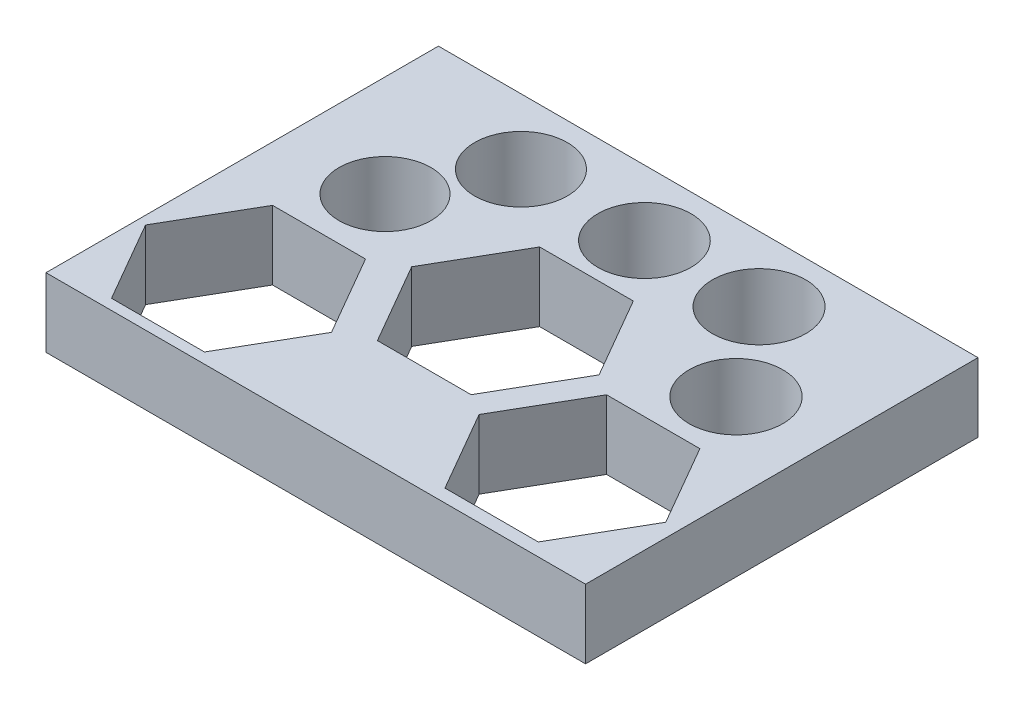
SolidWorks part; units mm, degrees
ref_plane "Front Plane" through (0, 0, 0) normal (0, 0, 1) x (1, 0, 0)
ref_plane "Top Plane" through (0, 0, 0) normal (0, 1, 0) x (1, 0, 0)
ref_plane "Right Plane" through (0, 0, 0) normal (1, 0, 0) x (0, 0, -1)
sketch "Sketch1" plane through (0, 0, 0) normal (0, 1, 0) x (1, 0, 0)
  line L1 (0, 0) -> (23.4547, 0)
  line L2 (0, 0) -> (0, 17.059)
  line L3 (0, 17.059) -> (23.4547, 17.059)
  line L4 (23.4547, 0) -> (23.4547, 17.059)
  line L5 (6.4297, 7.4595) -> (2.3883, 7.4595)
  line L6 (2.3883, 7.4595) -> (0.3676, 3.9595)
  line L7 (0.3676, 3.9595) -> (2.3883, 0.4595)
  line L8 (2.3883, 0.4595) -> (6.4297, 0.4595)
  line L9 (6.4297, 0.4595) -> (8.4505, 3.9595)
  line L10 (8.4505, 3.9595) -> (6.4297, 7.4595)
  line L11 (13.8319, 11.6985) -> (9.7604, 11.6985)
  line L12 (9.7604, 11.6985) -> (7.7247, 8.1725)
  line L13 (7.7247, 8.1725) -> (9.7604, 4.6465)
  line L14 (9.7604, 4.6465) -> (13.8319, 4.6465)
  line L15 (13.8319, 4.6465) -> (15.8676, 8.1725)
  line L16 (15.8676, 8.1725) -> (13.8319, 11.6985)
  line L17 (20.8364, 7.5879) -> (16.78, 7.5879)
  line L18 (16.78, 7.5879) -> (14.7517, 4.0749)
  line L19 (14.7517, 4.0749) -> (16.78, 0.562)
  line L20 (16.78, 0.562) -> (20.8364, 0.562)
  line L21 (20.8364, 0.562) -> (22.8646, 4.0749)
  line L22 (22.8646, 4.0749) -> (20.8364, 7.5879)
  circle A0 centre (4.409, 10.3275) radius 2
  circle A1 centre (6.4297, 14.2168) radius 2.015
  circle A2 centre (16.78, 14.2168) radius 2.03
  circle A3 centre (11.7962, 14.2168) radius 2.025
  circle A4 centre (19.6651, 10.3275) radius 2.035
  circle A5 centre (4.409, 3.9595) radius 4.0414 construction
  circle A6 centre (11.7962, 8.1725) radius 4.0714 construction
  circle A7 centre (18.8082, 4.0749) radius 4.0565 construction
  point P24 (22.2132, 3.0298)
  point P40 (14.5254, 7.4222)
  point P41 (5.1016, 4.5655)
  point P42 (4.409, 3.9595)
  point P43 (11.7962, 8.1725)
  point P44 (18.8082, 4.0749)
  point P45 (18.8082, 11.6985)
  point P46 (19.316, 11.1253)
  point P47 (4.008, 11.1253)
  point P48 (15.4766, 14.2168)
  point P49 (11.1883, 14.2168)
  point P50 (15.8676, 14.2168)
  point P51 (6.8502, 14.2168)
  point P52 (3.4097, 10.3275)
  point P53 (19.1665, 10.3275)
  point P54 (16.424, 14.2168)
  point P55 (6.4297, 14.2168)
  point P56 (11.7962, 14.2168)
  point P57 (16.78, 14.2168)
  point P58 (19.6651, 10.3275)
  point P59 (28.441, 16.6601)
  point P60 (4.409, 10.3275)
  point P61 (6.4297, 14.2168)
  point P62 (11.7962, 14.2168)
  point P63 (16.78, 14.2168)
  dimension "D1" = 4
  dimension "D2" = 4.03
  dimension "D3" = 4.06
  dimension "D4" = 4.05
  dimension "D5" = 4.07
  dimension "D6" = 8.0829
  dimension "D7" = 8.1429
  dimension "D8" = 8.1129
extrude "Boss-Extrude1" add sketch "Sketch1" along normal blind 3
